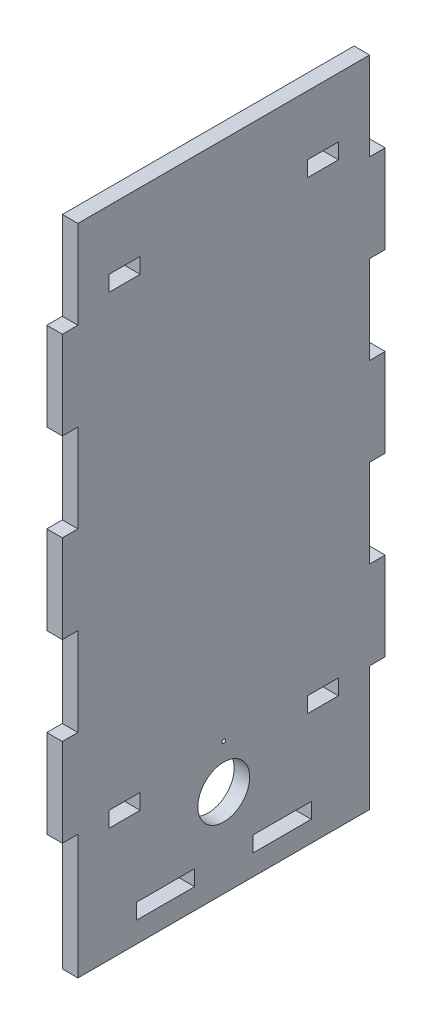
SolidWorks part; units mm, degrees
ref_plane "Front Plane" through (0, 0, 0) normal (0, 0, 1) x (1, 0, 0)
ref_plane "Top Plane" through (0, 0, 0) normal (0, 1, 0) x (1, 0, 0)
ref_plane "Right Plane" through (0, 0, 0) normal (1, 0, 0) x (0, 0, -1)
sketch "Sketch1" plane through (0, 0, 0) normal (1, 0, 0) x (0, 0, -1)
  line L1 (-56.25, -119) -> (56.25, -119)
  line L2 (-56.25, -119) -> (-56.25, 119)
  line L3 (-56.25, 119) -> (56.25, 119)
  line L4 (56.25, -119) -> (56.25, 119)
  line L5 (-56.25, -119) -> (56.25, 119) construction
  line L6 (-56.25, 119) -> (56.25, -119) construction
  point P0 (0, 0)
  dimension "D1" = 238
  dimension "D2" = 112.5
extrude "Boss-Extrude1" add sketch "Sketch1" along normal blind 6
sketch "Sketch2" plane through (6, 0, 0) normal (1, 0, 0) x (0, 0, -1)
  line L0 (0, -119) -> (0, -99) construction
  line L1 (0, -82.0294) -> (30.9706, -113) construction
  line L4 (56.25, -119) -> (56.25, 119)
  line L5 (56.25, 119) -> (-56.25, 119)
  line L6 (-56.25, 119) -> (-56.25, -119)
  line L7 (-56.25, -119) -> (56.25, -119)
  line L8 (56.25, -119) -> (56.25, 119) construction
  line L9 (56.25, 119) -> (-56.25, 119) construction
  line L10 (-56.25, 119) -> (-56.25, -119) construction
  line L11 (-56.25, -119) -> (56.25, -119) construction
  line L12 (0, -99) -> (0, -82.0294) construction
  line L13 (30.9706, -113) -> (0, -113) construction
  line L14 (0, -82.0294) -> (30.9706, -82.0294) construction
  line L15 (30.9706, -82.0294) -> (30.9706, -113) construction
  line L16 (0, -113) -> (0, -109) construction
  line L17 (8.4853, -90.5147) -> (7.0711, -91.9289) construction
  line L18 (0, -82.0294) -> (-16.9706, -82.0294) construction
  line L19 (-16.9706, -82.0294) -> (0, -65.0589) construction
  line L20 (0, -65.0589) -> (0, -82.0294) construction
  line L21 (0, -65.0589) -> (16.9706, -82.0294) construction
  line L22 (16.9706, -82.0294) -> (0, -99) construction
  line L23 (0, -99) -> (-16.9706, -82.0294) construction
  line L24 (-16.9706, -74.0294) -> (-16.9706, -90.0294) construction
  line L25 (-13.4706, -74.0294) -> (-13.4706, -90.0294)
  line L26 (-20.4706, -74.0294) -> (-20.4706, -90.0294)
  line L27 (0, -65.0589) -> (0, -60.5589) construction
  line L28 (0, -60.5589) -> (-4.5, -60.5589) construction
  line L29 (-4.5, -60.5589) -> (-4.5, -65.0589) construction
  circle A2 centre (0, -82.0294) radius 30.9706
  circle A3 centre (0, -99) radius 10
  circle A4 centre (-16.9706, -82.0294) radius 10 construction
  circle A5 centre (0, -65.0589) radius 10 construction
  arc A7 (-13.4706, -74.0294) -> (-20.4706, -74.0294) centre (-16.9706, -74.0294) ccw
  arc A8 (-20.4706, -90.0294) -> (-13.4706, -90.0294) centre (-16.9706, -90.0294) ccw
  circle A10 centre (-4.5, -60.5589) radius 1.4
  circle A11 centre (0, -60.5589) radius 1.4
  circle A12 centre (4.5, -60.5589) radius 1.4
  circle A15 centre (0, -65.0589) radius 1.4
  circle A16 centre (4.5, -65.0589) radius 1.4
  circle A19 centre (0, -69.5589) radius 1.4
  circle A20 centre (4.5, -69.5589) radius 1.4
  circle A31 centre (-4.5, -65.0589) radius 1.4
  circle A32 centre (-4.5, -69.5589) radius 1.4
  circle A35 centre (0, -82.0294) radius 0.75
  point P19 (-16.9706, -82.0294)
  dimension "D2" = 20
  dimension "D8" = 2.8
  dimension "D12" = 4.5
  dimension "D14" = 1.5
  dimension "D3" = 6
  dimension "D4" = 2
  dimension "D5" = 4
  dimension "D6" = 7
  dimension "D7" = 16
  dimension "D9" = 4.5
  dimension "D13" = 4.5
  dimension "D1" = 0
  dimension "D10" = 3
  dimension "D11" = 3
extrude "Cut-Extrude1" cut sketch "Sketch2" against normal blind 6 contours A3 | A35
sketch "Sketch3" plane through (6, 0, 0) normal (1, 0, 0) x (0, 0, -1)
  line L0 (-56.25, 119) -> (-56.25, -119) construction
  line L2 (-56.25, -89) -> (-56.25, -83) construction
  line L3 (-56.25, -83) -> (56.25, -83) construction
  line L4 (56.25, -89) -> (56.25, -83) construction
  line L5 (56.25, -119) -> (56.25, 119) construction
  line L6 (-44.25, -89) -> (-56.25, -89) construction
  line L7 (-44.25, -83) -> (-32.25, -83)
  line L8 (-44.25, -83) -> (-44.25, -89)
  line L9 (-44.25, -89) -> (-32.25, -89)
  line L10 (-32.25, -83) -> (-32.25, -89)
  line L11 (32.25, -89) -> (44.25, -89)
  line L12 (32.25, -89) -> (32.25, -83)
  line L13 (32.25, -83) -> (44.25, -83)
  line L14 (44.25, -89) -> (44.25, -83)
  line L15 (-32.25, -89) -> (32.25, -89)
  line L16 (44.25, -89) -> (56.25, -89)
  line L17 (-56.25, -119) -> (56.25, -119) construction
  dimension "D1" = 6
  dimension "D2" = 12
  dimension "D3" = 12
  dimension "D4" = 36
extrude "Cut-Extrude2" cut sketch "Sketch3" against normal blind 6 contours L10 L7 L8 L9 | L11 L14 L13 L12
sketch "Sketch4" plane through (0, -119, 0) normal (0, -1, 0) x (1, 0, 0)
  line L0 (6, 56.25) -> (6, -56.25) construction
  line L1 (0, -56.25) -> (6, -56.25)
  line L2 (0, -56.25) -> (0, -33.75)
  line L3 (0, -33.75) -> (6, -33.75)
  line L4 (6, -56.25) -> (6, -33.75)
  line L5 (0, 56.25) -> (0, -56.25) construction
  line L6 (6, -33.75) -> (0, -33.75) construction
  line L7 (6, -33.75) -> (6, -11.25) construction
  line L8 (6, -11.25) -> (0, -11.25) construction
  line L9 (0, -33.75) -> (0, -11.25) construction
  line L11 (6, 11.25) -> (0, 11.25)
  line L12 (6, 11.25) -> (6, -11.25)
  line L13 (6, -11.25) -> (0, -11.25)
  line L14 (0, 11.25) -> (0, -11.25)
  line L15 (0, 11.25) -> (6, 11.25) construction
  line L16 (0, 11.25) -> (0, 33.75) construction
  line L17 (0, 33.75) -> (6, 33.75) construction
  line L18 (6, 11.25) -> (6, 33.75) construction
  line L19 (6, 33.75) -> (0, 33.75)
  line L20 (6, 33.75) -> (6, 56.25)
  line L21 (6, 56.25) -> (0, 56.25)
  line L22 (0, 33.75) -> (0, 56.25)
extrude "Boss-Extrude2" add sketch "Sketch4" along normal blind 6
sketch "Sketch5" plane through (6, 0, 0) normal (1, 0, 0) x (0, 0, -1)
  line L0 (56.25, 90) -> (44.25, 90) construction
  line L1 (-32.25, 90) -> (-44.25, 90)
  line L2 (-32.25, 90) -> (-32.25, 96)
  line L3 (-32.25, 96) -> (-44.25, 96)
  line L4 (-44.25, 90) -> (-44.25, 96)
  line L5 (56.25, 96) -> (44.25, 96) construction
  line L6 (-32.25, 90) -> (-32.25, -83) construction
  line L7 (44.25, 90) -> (32.25, 90)
  line L8 (44.25, 90) -> (44.25, 96)
  line L9 (44.25, 96) -> (32.25, 96)
  line L10 (32.25, 90) -> (32.25, 96)
  line L11 (-44.25, 90) -> (-44.25, -83)
  line L12 (-44.25, 90) -> (44.25, 90)
  line L13 (0, 90) -> (0, 0)
  line L22 (56.25, -125) -> (56.25, 119)
  line L23 (56.25, 119) -> (-56.25, 119)
  line L24 (-56.25, 119) -> (-56.25, -125)
  line L25 (-56.25, -125) -> (-33.75, -125)
  line L26 (-33.75, -125) -> (-33.75, -119)
  line L27 (-33.75, -119) -> (-11.25, -119)
  line L28 (-11.25, -119) -> (-11.25, -125)
  line L29 (-11.25, -125) -> (11.25, -125)
  line L30 (11.25, -125) -> (11.25, -119)
  line L31 (11.25, -119) -> (33.75, -119)
  line L32 (33.75, -119) -> (33.75, -125)
  line L33 (33.75, -125) -> (56.25, -125)
  line L34 (56.25, -125) -> (56.25, 119)
  line L35 (56.25, 119) -> (-56.25, 119)
  line L36 (-56.25, 119) -> (-56.25, -125)
  line L37 (-56.25, -125) -> (-33.75, -125)
  line L38 (-33.75, -125) -> (-33.75, -119)
  line L39 (-33.75, -119) -> (-11.25, -119)
  line L40 (-11.25, -119) -> (-11.25, -125)
  line L41 (-11.25, -125) -> (11.25, -125)
  line L42 (11.25, -125) -> (11.25, -119)
  line L43 (11.25, -119) -> (33.75, -119)
  line L44 (33.75, -119) -> (33.75, -125)
  line L45 (33.75, -125) -> (56.25, -125)
  dimension "D1" = 0
extrude "Cut-Extrude3" cut sketch "Sketch5" against normal blind 6 contours L4 L1 L2 L3 | L10 L7 L8 L9
sketch "Sketch6" plane through (0, 0, -56.25) normal (0, 0, -1) x (-1, 0, 0)
  line L33 (-6, -125) -> (-6, 119) construction
  line L34 (0, 119) -> (-6, 119)
  line L35 (0, 119) -> (0, 85)
  line L36 (0, 85) -> (-6, 85)
  line L37 (-6, 119) -> (-6, 85)
  line L38 (0, -125) -> (0, 119) construction
  line L39 (-6, 85) -> (0, 85)
  line L40 (-6, 85) -> (-6, 51)
  line L41 (-6, 51) -> (0, 51)
  line L42 (0, 85) -> (0, 51)
  line L43 (0, -125) -> (-6, -125) construction
  line L44 (0, 51) -> (-6, 51)
  line L45 (0, 51) -> (0, 17)
  line L46 (0, 17) -> (-6, 17)
  line L47 (-6, 51) -> (-6, 17)
  line L48 (-6, 17) -> (0, 17)
  line L49 (-6, 17) -> (-6, -17)
  line L50 (-6, -17) -> (0, -17)
  line L51 (0, 17) -> (0, -17)
  line L52 (0, -17) -> (-6, -17)
  line L53 (0, -17) -> (0, -51)
  line L54 (0, -51) -> (-6, -51)
  line L55 (-6, -17) -> (-6, -51)
  line L56 (-6, -51) -> (0, -51)
  line L57 (-6, -51) -> (-6, -85)
  line L58 (-6, -85) -> (0, -85)
  line L59 (0, -51) -> (0, -85)
  line L60 (0, -85) -> (-6, -85)
  line L61 (0, -85) -> (0, -119)
  line L62 (0, -119) -> (-6, -119)
  line L63 (-6, -85) -> (-6, -119)
  line L64 (-6, -119) -> (0, -119)
  line L65 (-6, -119) -> (-6, -125)
  line L66 (-6, -125) -> (0, -125) construction
  line L67 (0, -119) -> (0, -125) construction
  line L68 (0, -125) -> (-6, -125)
extrude "Boss-Extrude3" add sketch "Sketch6" along normal blind 6
mirror "Mirror1" about plane through (0, 0, 0) normal (0, 0, 1) of "Boss-Extrude3"
sketch "Sketch7" plane through (0, -125, 0) normal (0, -1, 0) x (-1, 0, 0)
  line L1 (0, 56.25) -> (-6, 56.25)
  line L2 (0, 56.25) -> (0, -56.25)
  line L3 (0, -56.25) -> (-6, -56.25)
  line L4 (-6, 56.25) -> (-6, -56.25)
extrude "Boss-Extrude4" add sketch "Sketch7" along normal blind 8
